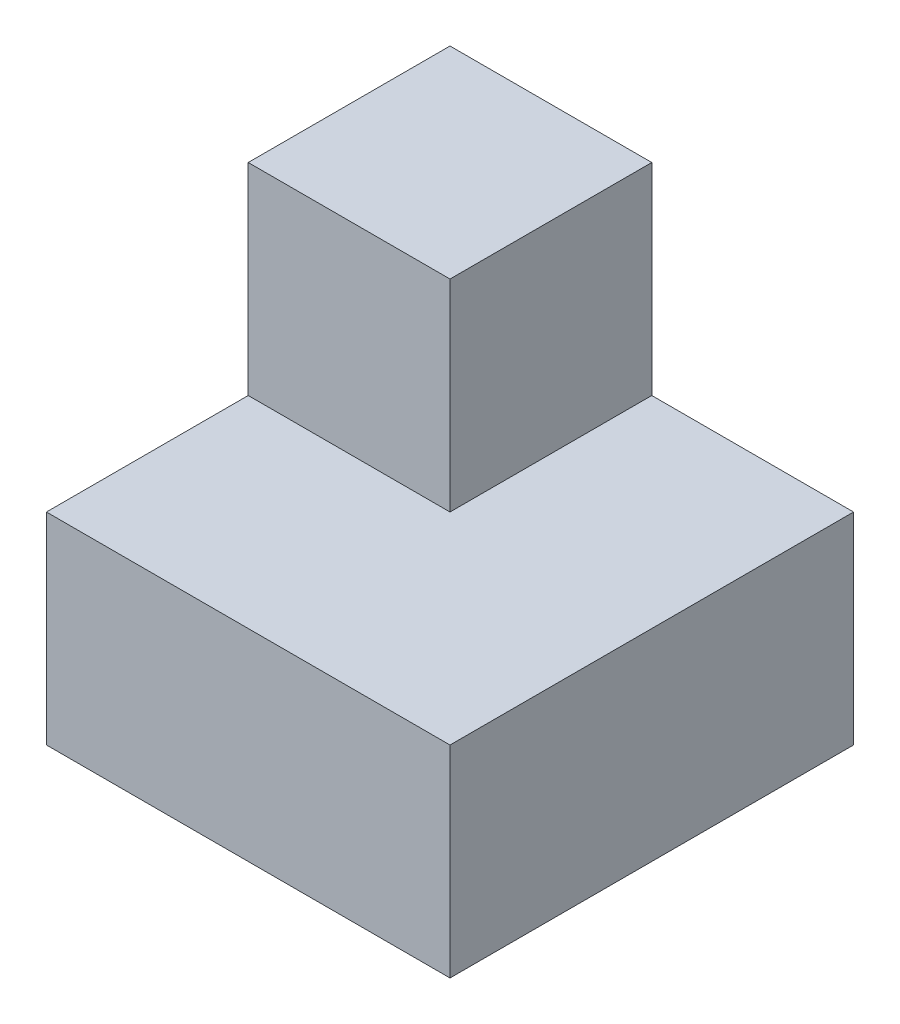
SolidWorks part; units mm, degrees
ref_plane "Front" through (0, 0, 0) normal (0, 0, 1) x (1, 0, 0)
ref_plane "Top" through (0, 0, 0) normal (0, 1, 0) x (1, 0, 0)
ref_plane "Right" through (0, 0, 0) normal (1, 0, 0) x (0, 0, -1)
sketch "Sketch1" plane through (0, 0, 0) normal (0, 1, 0) x (1, 0, 0)
  line L1 (0, 0) -> (4, 0)
  line L2 (0, 0) -> (0, 4)
  line L3 (0, 4) -> (4, 4)
  line L4 (4, 0) -> (4, 4)
  dimension "D1" = 4
  dimension "D2" = 4
extrude "Boss-Extrude1" add sketch "Sketch1" along normal blind 4
sketch "Sketch2" plane through (0, 4, 0) normal (0, 1, 0) x (1, 0, 0)
  line L5 (0, 4) -> (2, 4)
  line L6 (0, 4) -> (0, 2)
  line L7 (0, 2) -> (2, 2)
  line L8 (2, 4) -> (2, 2)
  line M1 (0, 4) -> (0, 0)
  line M2 (0, 0) -> (4, 0)
  line M3 (4, 0) -> (4, 4)
  line M4 (4, 4) -> (0, 4)
  dimension "D1" = 2
  dimension "D2" = 2
extrude "Cut-Extrude1" cut sketch "Sketch2" against normal blind 2 contours L8 L7 M4 M1 M2 M3
